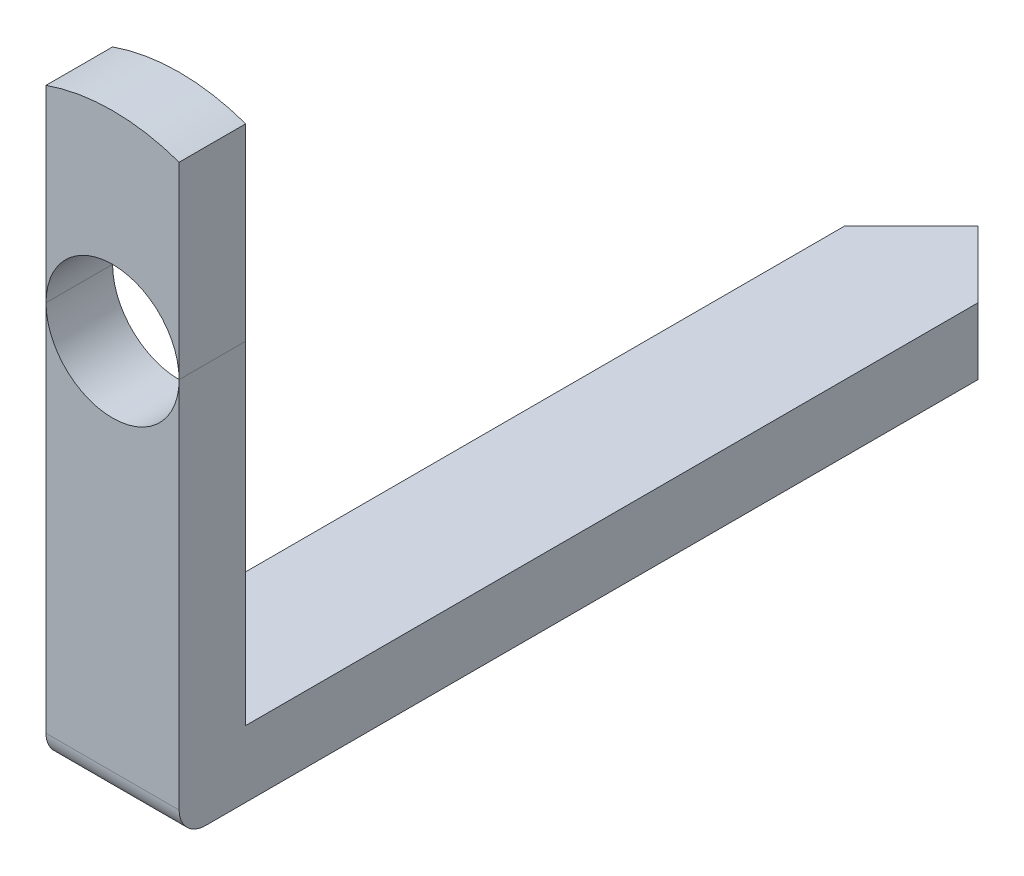
SolidWorks part; units mm, degrees
material "Alliage 1060"
ref_plane "Plan de face" through (0, 0, 0) normal (0, 0, 1) x (1, 0, 0)
ref_plane "Plan de dessus" through (0, 0, 0) normal (0, 1, 0) x (1, 0, 0)
ref_plane "Plan de droite" through (0, 0, 0) normal (1, 0, 0) x (0, 0, -1)
sketch "Esquisse1" plane through (0, 0, 0) normal (0, 0, 1) x (1, 0, 0)
  line L0 (-2.0797, 0) -> (1.8994, 0) construction
  line L1 (0, 1.8722) -> (0, -3.0342) construction
  line L2 (-1.5, 0) -> (-1.5, -3)
  line L3 (1.5, 0) -> (1.5, -3)
  line L4 (1.5, -3) -> (-1.5, -3)
  circle A0 centre (0, 0) radius 0.5
  arc A1 (1.5, 0) -> (-1.5, 0) centre (0, 0) ccw
  dimension "D1" = 3
  dimension "D2" = 1
  dimension "D3" = 3
extrude "Boss.-Extru.1" add sketch "Esquisse1" along normal blind 0.5
sketch "Esquisse2" plane through (0, -3, 0) normal (0, -1, 0) x (1, 0, 0)
  line L0 (-1.5, 0.5) -> (1.5, 0.5)
  line L1 (1.5, 0.5) -> (1.5, -1)
  line L2 (1.5, -1) -> (0.5, -1)
  line L3 (0.5, -1) -> (0.5, -5.5)
  line L4 (-1.5, 0.5) -> (-1.5, -1)
  line L5 (-1.5, -1) -> (-0.5, -1)
  line L6 (-0.5, -1) -> (-0.5, -5.5)
  line L7 (0, 0.7417) -> (0, -6.3973) construction
  line L8 (-0.5, -5.5) -> (0, -6)
  line L9 (0, -6) -> (0.5, -5.5)
  line L10 (0.9499, -5.5) -> (-0.7457, -5.5) construction
  dimension "D1" = 1.5
  dimension "D2" = 1
  dimension "D3" = 5
  dimension "D4" = 45
extrude "Boss.-Extru.2" add sketch "Esquisse2" against normal blind 0.5
fillet "Congé1" radius 0.2 1 edges at (0, -3, 0.5)
sketch "Esquisse3" plane through (0, -3, 0) normal (0, -1, 0) x (1, 0, 0)
  line L0 (-0.5, -1) -> (-0.5, -5.5) construction
  line L1 (-0.5, -1.2499) -> (-2.5243, -1.2499)
  line L2 (-0.5, -1.2499) -> (-0.5, 1.0098)
  line L3 (-0.5, 1.0098) -> (0.5, 1.0098)
  line L4 (-2.5243, -1.2499) -> (-2.5243, 1.0098)
  line L5 (0.5, -5.5) -> (0.5, -1) construction
  line L6 (0.5, -1.2499) -> (1.9136, -1.2499)
  line L7 (0.5, -1.2499) -> (0.5, 1.0098)
  line L8 (-2.5243, 1.0098) -> (0.1832, 1.417)
  line L9 (1.9136, -1.2499) -> (1.9136, 1.0098)
  line L10 (0.1832, 1.417) -> (1.9136, 1.0098)
extrude "Enlèv. mat.-Extru.1" cut sketch "Esquisse3" against normal through all
